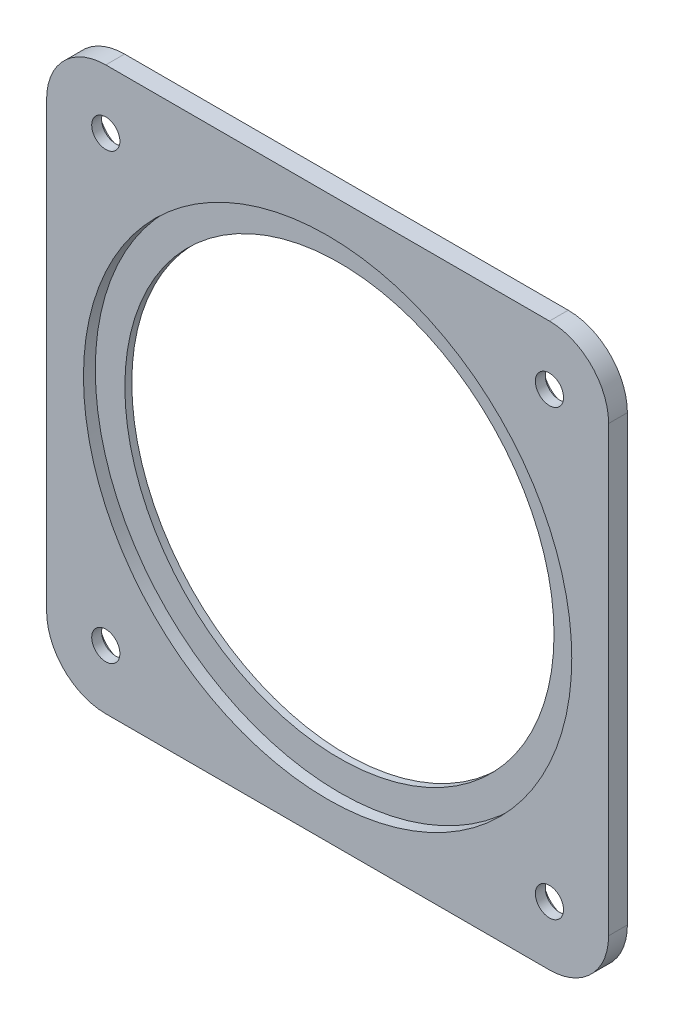
SolidWorks part; units mm, degrees
ref_plane "Front Plane" through (0, 0, 0) normal (0, 0, 1) x (1, 0, 0)
ref_plane "Top Plane" through (0, 0, 0) normal (0, 1, 0) x (1, 0, 0)
ref_plane "Right Plane" through (0, 0, 0) normal (1, 0, 0) x (0, 0, -1)
sketch "Sketch1" plane through (0, 0, 0) normal (0, 0, 1) x (1, 0, 0)
  line L1 (-75, -95) -> (75, -95)
  line L2 (-95, -75) -> (-95, 75)
  line L3 (-75, 95) -> (75, 95)
  line L4 (95, -75) -> (95, 75)
  line L5 (-95, -95) -> (95, 95) construction
  line L6 (-95, 95) -> (95, -95) construction
  circle A0 centre (0, 0) radius 72.55
  arc A1 (75, -95) -> (95, -75) centre (75, -75) ccw
  arc A2 (-75, -95) -> (-95, -75) centre (-75, -75) cw
  arc A3 (75, 95) -> (95, 75) centre (75, 75) cw
  arc A4 (-95, 75) -> (-75, 95) centre (-75, 75) cw
  circle A5 centre (-75, 75) radius 4.7625
  circle A6 centre (75, 75) radius 4.7625
  circle A7 centre (75, -75) radius 4.7625
  circle A8 centre (-75, -75) radius 4.7625
  point P0 (0, 0)
  point P31 (0, 0)
  dimension "D3" = 145.1
  dimension "D4" = 20
  dimension "D5" = 9.525
  dimension "D1" = 190
  dimension "D2" = 190
  dimension "D6" = 20
  dimension "D7" = 4
extrude "Boss-Extrude1" add sketch "Sketch1" along normal blind 6.35
sketch "Sketch2" plane through (0, 0, 6.35) normal (0, 0, 1) x (1, 0, 0)
  circle A0 centre (0, 0) radius 82.55
  dimension "D1" = 165.1
extrude "Cut-Extrude1" cut sketch "Sketch2" against normal blind 4
sketch "Sketch3" plane through (0, 0, 0) normal (0, 0, -1) x (-1, 0, 0)
  line L0 (95, 75) -> (95, -75) construction
  line L1 (-75, 95) -> (75, 95) construction
  line L2 (75, -95) -> (-75, -95) construction
  circle A0 centre (-75, 75) radius 8.5
  circle A4 centre (75, 75) radius 8.5
  circle A5 centre (75, -75) radius 8.5
  circle A6 centre (-75, -75) radius 8.5
  point P12 (1.3909, -1.3909)
  point P17 (0, 0)
  dimension "D1" = 17
  dimension "D3" = 20
  dimension "D4" = 20
  dimension "D5" = 20
  dimension "D2" = 4
extrude "Cut-Extrude2" cut sketch "Sketch3" against normal blind 3
